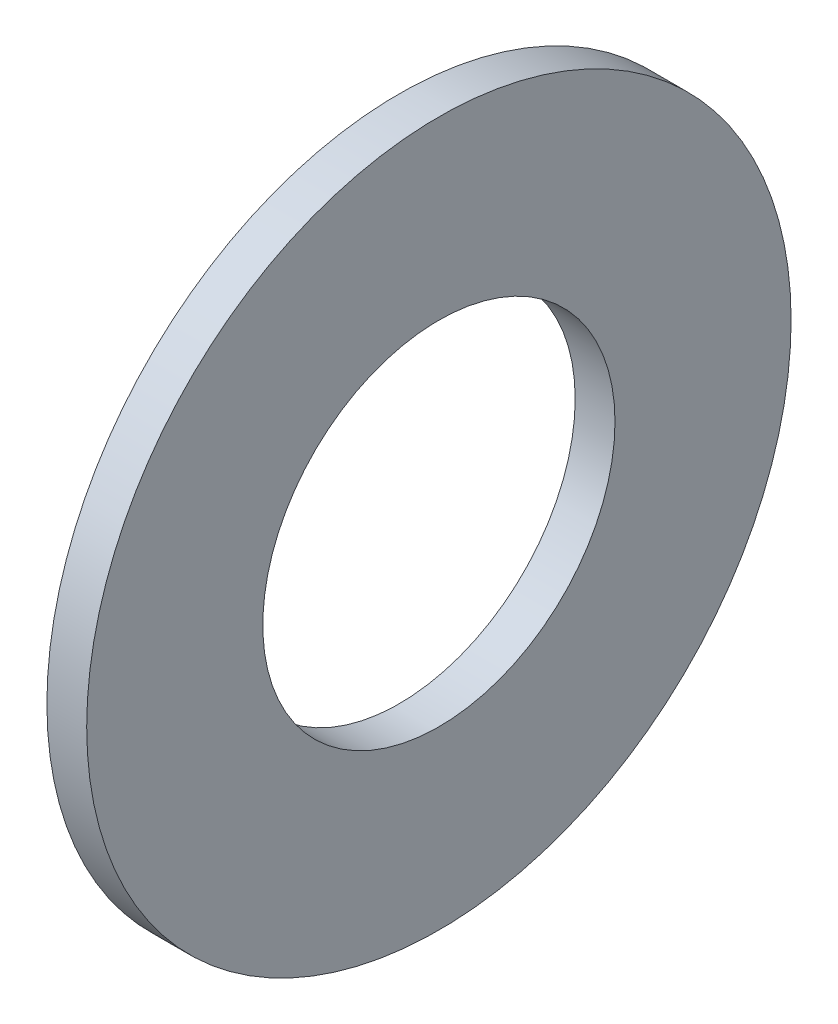
SolidWorks part; units mm, degrees
ref_plane "Front Plane" through (0, 0, 0) normal (0, 0, 1) x (1, 0, 0)
ref_plane "Top Plane" through (0, 0, 0) normal (0, 1, 0) x (1, 0, 0)
ref_plane "Right Plane" through (0, 0, 0) normal (1, 0, 0) x (0, 0, -1)
sketch "Sketch1" plane through (0, 0, 0) normal (1, 0, 0) x (0, 0, -1)
  circle A0 centre (0, 0) radius 13.4874
  circle A1 centre (0, 0) radius 6.7437
  dimension "OD" = 26.9748
  dimension "ID" = 13.4874
extrude "Boss-Extrude2" add sketch "Sketch1" along normal blind 1.524
